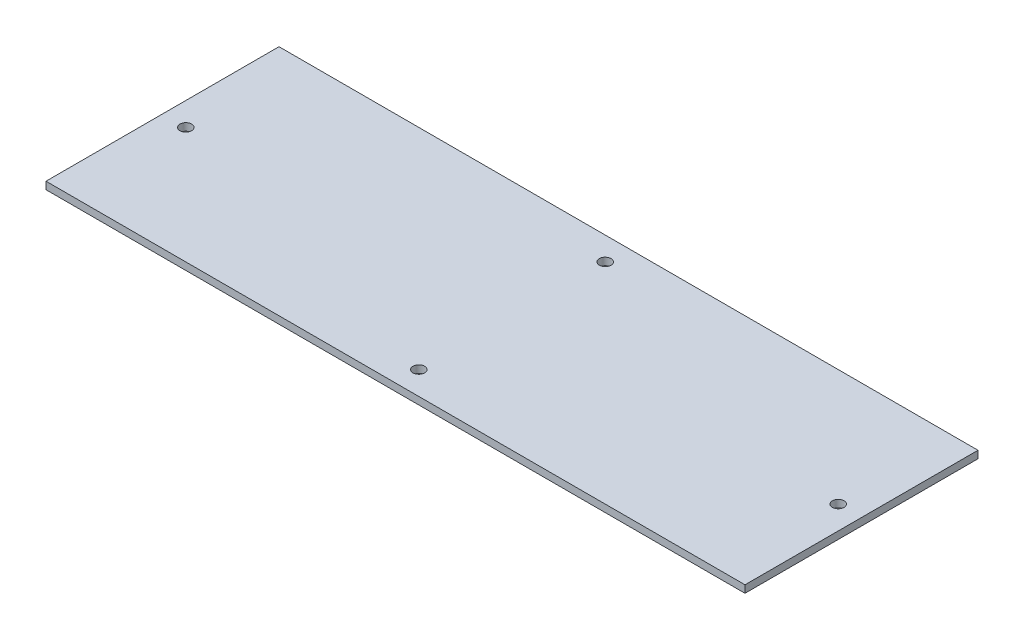
SolidWorks part; units mm, degrees
ref_plane "Front Plane" through (0, 0, 0) normal (0, 0, 1) x (1, 0, 0)
ref_plane "Top Plane" through (0, 0, 0) normal (0, 1, 0) x (1, 0, 0)
ref_plane "Right Plane" through (0, 0, 0) normal (1, 0, 0) x (0, 0, -1)
sketch "Sketch1" plane through (0, 0, 0) normal (0, 1, 0) x (1, 0, 0)
  line L1 (0, 0) -> (300, 0)
  line L2 (0, 0) -> (0, 100)
  line L3 (0, 100) -> (300, 100)
  line L4 (300, 0) -> (300, 100)
  circle A0 centre (150, 10) radius 2.5
  circle A1 centre (10, 50) radius 2.5
  circle A2 centre (150, 90) radius 2.5
  circle A3 centre (290, 50) radius 2.5
  point P14 (150, 100)
  point P16 (300, 50)
  point P18 (150, 0)
  point P20 (0, 50)
  dimension "D3" = 5
  dimension "D4" = 10
  dimension "D5" = 10
  dimension "D6" = 10
  dimension "D7" = 10
  dimension "D1" = 100
  dimension "D2" = 300
extrude "Boss-Extrude1" add sketch "Sketch1" along normal blind 3.175
